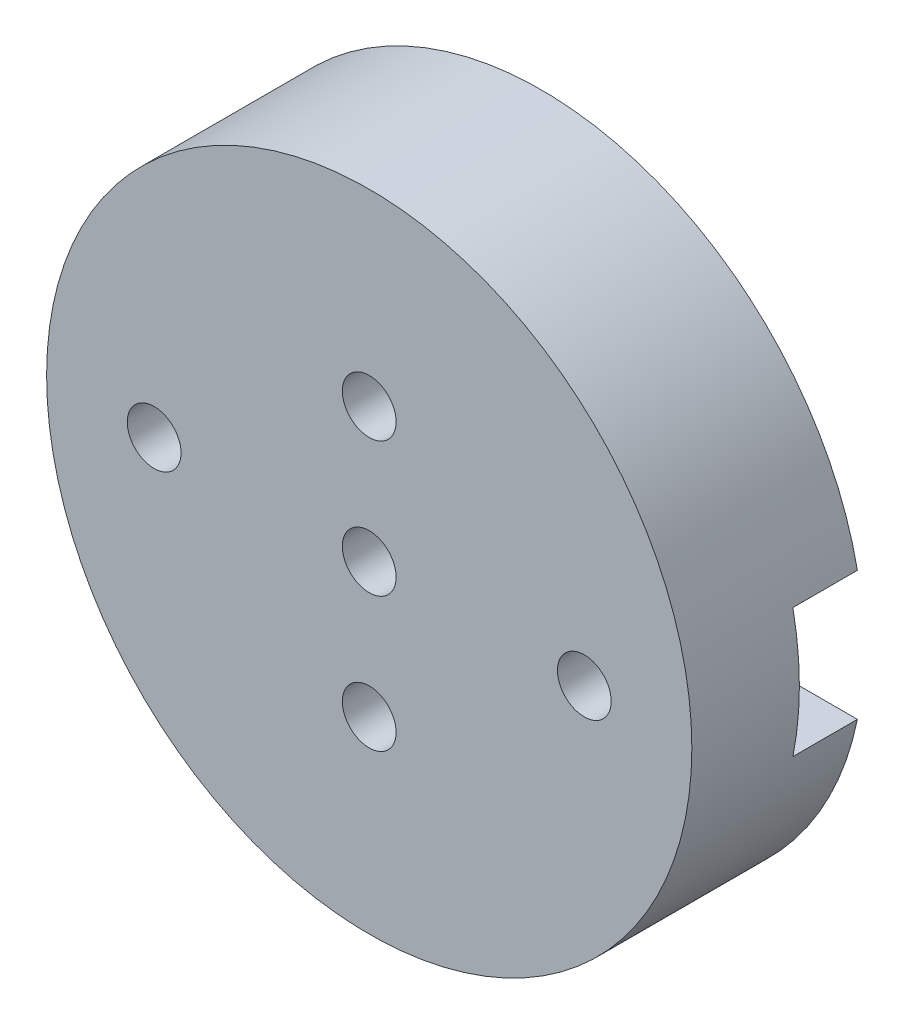
SolidWorks part; units mm, degrees
material "Brass"
ref_plane "Front Plane" through (0, 0, 0) normal (0, 0, 1) x (1, 0, 0)
ref_plane "Top Plane" through (0, 0, 0) normal (0, 1, 0) x (1, 0, 0)
ref_plane "Right Plane" through (0, 0, 0) normal (1, 0, 0) x (0, 0, -1)
sketch "Sketch2" plane through (0, 0, 0) normal (0, 0, 1) x (1, 0, 0)
  line L0 (-104.8152, 0) -> (123.7302, 0) construction
  line L1 (0, 101.8229) -> (0, -118.5601) construction
  line L2 (0, 0) -> (40, 0) construction
  line L3 (0, 0) -> (-40, 0) construction
  line L4 (0, 0) -> (0, 25) construction
  line L5 (0, 0) -> (0, -25) construction
  circle A0 centre (0, 0) radius 60
  circle A1 centre (0, 0) radius 5
  circle A2 centre (40, 0) radius 5
  circle A3 centre (-40, 0) radius 5
  circle A4 centre (0, 25) radius 5
  circle A5 centre (0, -25) radius 5
  dimension "D1" = 120
  dimension "D2" = 10
  dimension "D4" = 40
  dimension "D6" = 40
  dimension "D8" = 25
  dimension "D10" = 25
  dimension "D3" = 2
  dimension "D5" = 2
  dimension "D7" = 2
  dimension "D9" = 2
extrude "Boss-Extrude1" add sketch "Sketch2" along normal blind 32
sketch "Sketch4" plane through (0, 0, 0) normal (0, 0, 1) x (1, 0, 0)
  line L1 (12, 25) -> (12, 12)
  line L2 (-12, 25) -> (-12, 12)
  line L3 (-66.5122, 12) -> (-12, 12)
  line L4 (-66.5122, 12) -> (-66.5122, -12)
  line L5 (-66.5122, -12) -> (-12, -12)
  line L6 (66.5122, 12) -> (66.5122, -12)
  line L7 (-12, -12) -> (-12, -25)
  line L8 (12, -12) -> (12, -25)
  line L23 (12, 12) -> (66.5122, 12)
  line L24 (12, -12) -> (66.5122, -12)
  arc A0 (12, 25) -> (-12, 25) centre (0, 25) ccw
  circle A1 centre (0, 0) radius 60
  arc A2 (-58.7878, -12) -> (58.7878, -12) centre (0, 0) ccw
  arc A6 (-12, -25) -> (12, -25) centre (0, -25) ccw
  point P0 (0, 0)
  point P20 (0, 0)
  dimension "D4" = 50
  dimension "D2" = 24
  dimension "D3" = 24
  dimension "D1" = 0
extrude "Cut-Extrude2" cut sketch "Sketch4" along normal blind 12
sketch "Sketch5" plane through (0, 0, 0) normal (0, 0, 1) x (1, 0, 0)
  line L1 (88.0365, 0) -> (60, 0) construction
  line L6 (49, 0) -> (-49, 0) construction
  line L9 (-60, 0) -> (-130.0938, 0) construction
  arc A0 (29.5865, -39.0594) -> (29.5958, 39.0524) centre (0, 0) ccw
  arc A1 (-58.7878, -12) -> (58.7878, -12) centre (0, 0) ccw construction
  arc A2 (27.6133, 47.5658) -> (-27.3865, 47.6967) centre (0, 0) ccw
  arc A3 (58.7878, -12) -> (58.7878, 12) centre (0, 0) ccw construction
  arc A4 (21.5886, 37.1878) -> (-21.4113, 37.2902) centre (0, 0) ccw
  arc A5 (-58.7878, 12) -> (-58.7878, -12) centre (0, 0) ccw construction
  arc A6 (58.7878, 12) -> (-58.7878, 12) centre (0, 0) ccw construction
  arc A7 (21.5886, 37.1878) -> (27.6133, 47.5658) centre (24.6009, 42.3768) ccw
  arc A9 (-58.7878, -12) -> (58.7878, -12) centre (0, 0) ccw
  arc A11 (58.7878, -12) -> (58.7878, 12) centre (0, 0) ccw
  arc A13 (-58.7878, 12) -> (-58.7878, -12) centre (0, 0) ccw
  arc A14 (0, 60) -> (-58.7878, 12) centre (0, 0) ccw
  arc A16 (-29.4095, 39.1929) -> (-29.4002, -39.1998) centre (0, 0) ccw
  arc A17 (-27.3865, 47.6967) -> (-21.4113, 37.2902) centre (-24.3989, 42.4934) ccw
  arc A19 (27.6917, -47.7008) -> (-27.4643, -47.8321) centre (0, 0) cw
  arc A20 (21.667, -37.3229) -> (-21.489, -37.4256) centre (0, 0) cw
  arc A21 (21.667, -37.3229) -> (27.6917, -47.7008) centre (24.6793, -42.5118) cw
  arc A22 (-27.4643, -47.8321) -> (-21.489, -37.4256) centre (-24.4767, -42.6289) cw
  point P19 (0.1166, 48.9999)
  point P31 (0.1166, -48.9999)
  dimension "D1" = 98
  dimension "D2" = 6
  dimension "D4" = 6
  dimension "D3" = 60
extrude "Cut-Extrude3" cut sketch "Sketch5" along normal blind 12 contours A2 A17 A4 A7 | A22 A19 A21 A20
ref_plane "Plane1" through (0, 0, 32) normal (0, 0, 1) x (1, 0, 0)
